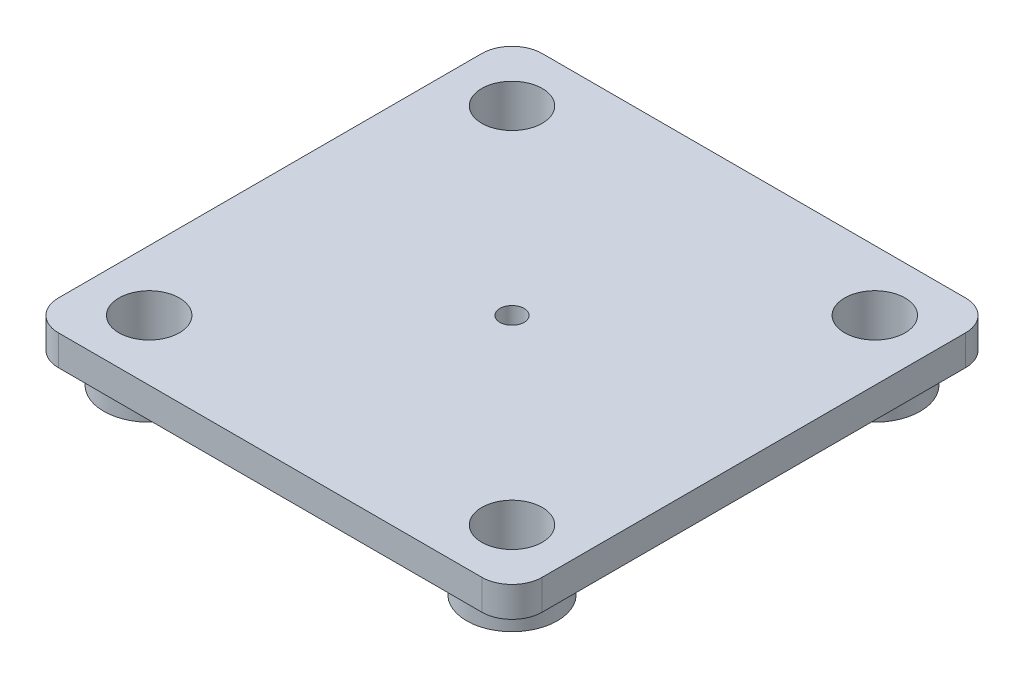
SolidWorks part; units mm, degrees
ref_plane "Front" through (0, 0, 0) normal (0, 0, 1) x (1, 0, 0)
ref_plane "Top" through (0, 0, 0) normal (0, 1, 0) x (1, 0, 0)
ref_plane "Right" through (0, 0, 0) normal (1, 0, 0) x (0, 0, -1)
sketch "Sketch1" plane through (0, 0, 0) normal (0, 1, 0) x (1, 0, 0)
  line L1 (-40, 40) -> (40, 40)
  line L2 (-40, 40) -> (-40, -40)
  line L3 (-40, -40) -> (40, -40)
  line L4 (40, 40) -> (40, -40)
  line L5 (-40, 40) -> (40, -40) construction
  line L6 (-40, -40) -> (40, 40) construction
  line L7 (-30, 30) -> (30, 30) construction
  line L8 (-30, 30) -> (-30, -30) construction
  line L9 (-30, -30) -> (30, -30) construction
  line L10 (30, 30) -> (30, -30) construction
  line L11 (-30, 30) -> (30, -30) construction
  line L12 (-30, -30) -> (30, 30) construction
  circle A0 centre (-30, 30) radius 5
  circle A1 centre (30, 30) radius 5
  circle A2 centre (30, -30) radius 5
  circle A3 centre (-30, -30) radius 5
  point P0 (0, 0)
  point P6 (0, 0)
  dimension "D3" = 10
  dimension "D1" = 60
  dimension "D2" = 10
extrude "Boss-Extrude1" add sketch "Sketch1" along normal blind 5
sketch "Sketch2" plane through (0, 0, 0) normal (0, -1, 0) x (1, 0, 0)
  circle A0 centre (-30, -30) radius 5 construction
  circle A1 centre (30, -30) radius 5 construction
  circle A2 centre (30, 30) radius 5 construction
  circle A3 centre (-30, 30) radius 5 construction
  circle A4 centre (-30, -30) radius 5
  circle A5 centre (30, -30) radius 5
  circle A6 centre (30, 30) radius 5
  circle A7 centre (-30, 30) radius 5
extrude "Extrude-Thin1" add sketch "Sketch2" along normal blind 5 thin
sketch "Sketch3" plane through (0, 5, 0) normal (0, 1, 0) x (1, 0, 0)
  circle A0 centre (0, 0) radius 2
  dimension "D1" = 4
extrude "Cut-Extrude1" cut sketch "Sketch3" against normal through all
fillet "Fillet1" radius 5 4 edges at (-40, 2.5, 40) (-40, 2.5, -40) (40, 2.5, 40) (40, 2.5, -40)
